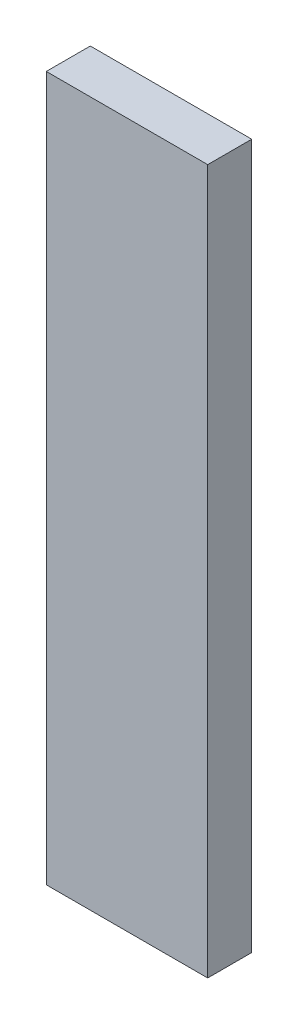
SolidWorks part; units mm, degrees
material "Oak"
ref_plane "Front Plane" through (0, 0, 0) normal (0, 0, 1) x (1, 0, 0)
ref_plane "Top Plane" through (0, 0, 0) normal (0, 1, 0) x (1, 0, 0)
ref_plane "Right Plane" through (0, 0, 0) normal (1, 0, 0) x (0, 0, -1)
sketch "Sketch1" plane through (0, 0, 0) normal (0, 1, 0) x (1, 0, 0)
  line L1 (-69.85, -19.05) -> (69.85, -19.05)
  line L2 (-69.85, -19.05) -> (-69.85, 19.05)
  line L3 (-69.85, 19.05) -> (69.85, 19.05)
  line L4 (69.85, -19.05) -> (69.85, 19.05)
  line L5 (-69.85, -19.05) -> (69.85, 19.05) construction
  line L6 (-69.85, 19.05) -> (69.85, -19.05) construction
  point P0 (0, 0)
  dimension "D1" = 38.1
  dimension "D2" = 139.7
extrude "Boss-Extrude1" add sketch "Sketch1" along normal blind 609.6 contours L3 L4 L1 L2
